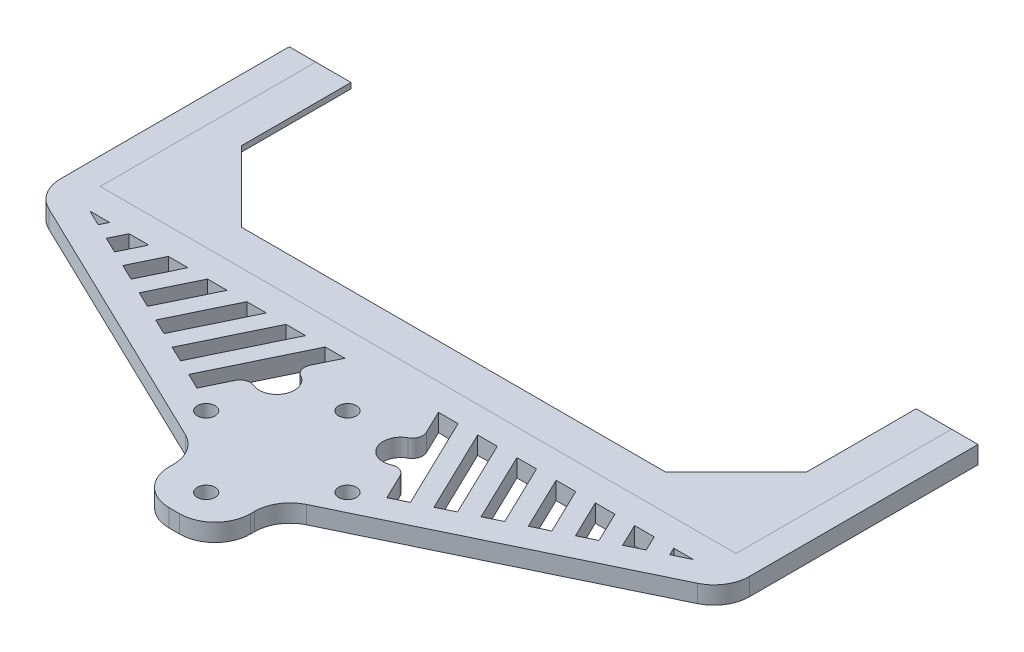
SolidWorks part; units mm, degrees
ref_plane "Front Plane" through (0, 0, 0) normal (0, 0, 1) x (1, 0, 0)
ref_plane "Top Plane" through (0, 0, 0) normal (0, 1, 0) x (1, 0, 0)
ref_plane "Right Plane" through (0, 0, 0) normal (1, 0, 0) x (0, 0, -1)
sketch "Sketch1" plane through (0, 0, 0) normal (0, 1, 0) x (1, 0, 0)
  line L0 (-114.3, 128.27) -> (-114.3, 50.8)
  line L1 (-114.3, 50.8) -> (114.3, 50.8)
  line L2 (114.3, 50.8) -> (114.3, 128.27)
  line L3 (114.3, 128.27) -> (123.825, 128.27)
  line L4 (123.825, 128.27) -> (123.825, 46.0729)
  line L5 (-114.3, 128.27) -> (-123.825, 128.27)
  line L6 (-123.825, 128.27) -> (-123.825, 46.0729)
  line L7 (0, 40) -> (0, -40) construction
  line L8 (-40, 0) -> (40, 0) construction
  line L9 (-28.2843, -28.2843) -> (28.2843, 28.2843) construction
  line L10 (-28.2843, 28.2843) -> (28.2843, -28.2843) construction
  line L11 (-116.6445, 34.635) -> (-21.7855, -11.14)
  line L13 (-14.605, -22.5779) -> (-14.605, -24.13)
  line L14 (-1.905, -36.83) -> (1.905, -36.83)
  line L15 (14.605, -24.13) -> (14.605, -22.5779)
  line L17 (21.7855, -11.14) -> (116.6445, 34.635)
  circle A0 centre (0, 0) radius 40 construction
  circle A1 centre (0, 0) radius 25.4 construction
  circle A2 centre (0, 0) radius 31.5 construction
  arc A3 (123.825, 46.0729) -> (116.6445, 34.635) centre (111.125, 46.0729) cw
  arc A4 (14.605, -22.5779) -> (21.7855, -11.14) centre (27.305, -22.5779) cw
  arc A5 (1.905, -36.83) -> (14.605, -24.13) centre (1.905, -24.13) ccw
  arc A6 (-14.605, -24.13) -> (-1.905, -36.83) centre (-1.905, -24.13) ccw
  arc A7 (-21.7855, -11.14) -> (-14.605, -22.5779) centre (-27.305, -22.5779) cw
  arc A8 (-123.825, 46.0729) -> (-116.6445, 34.635) centre (-111.125, 46.0729) ccw
  point P21 (0, 25.4)
  point P22 (25.4, 0)
  point P23 (0, -25.4)
  point P24 (-25.4, 0)
  point P25 (-22.2739, 22.2739)
  point P26 (-22.2739, -22.2739)
  point P27 (22.2739, -22.2739)
  point P28 (22.2739, 22.2739)
  point P37 (14.605, -14.605)
  point P40 (14.605, -36.83)
  point P43 (-14.605, -36.83)
  point P46 (-14.605, -14.605)
  point P49 (-123.825, 38.1)
  dimension "D4" = 80
  dimension "D5" = 50.8
  dimension "D6" = 63
  dimension "D13" = 12.7
  dimension "D1" = 247.65
  dimension "D2" = 9.525
  dimension "D3" = 9.525
  dimension "D7" = 45
  dimension "D8" = 77.47
  dimension "D9" = 29.21
  dimension "D10" = 50.8
  dimension "D11" = 11.43
  dimension "D12" = 12.7
extrude "Boss-Extrude1" add sketch "Sketch1" along normal blind 6.35
hole_wizard "M6 Clearance Hole1" positions "Sketch6" profile "Sketch5" hole size "M6" standard "ANSI Metric" end condition through all
sketch "Sketch6" plane through (0, 0, 0) normal (0, -1, 0) x (-1, 0, 0)
  point P0 (0, 25.4)
  point P3 (0, -25.4)
  point P6 (-25.4, 0)
  point P9 (25.4, 0)
sketch "Sketch5" plane through (0, 0, -25.4) normal (1, 0, 0) x (0, 0, -1)
  line L0 (0, 0) -> (0, 6.35)
  line L1 (0, 6.35) -> (3.2, 6.35)
  line L2 (3.2, 6.35) -> (3.2, 0)
  line L5 (3.2, 0) -> (0, 0)
  line L11 (0, -6.35) -> (0, 107.95) construction
  dimension "Thru Hole Dia." = 6.4
  dimension "Thru Hole Depth" = 6.35
sketch "Sketch7" plane through (0, 6.35, 0) normal (0, 1, 0) x (1, 0, 0)
  line L0 (-108.4879, 41.275) -> (-17.0471, -2.8505) construction
  line L1 (-108.4879, 41.275) -> (108.4879, 41.275) construction
  line L2 (108.4879, 41.275) -> (16.1645, -3.2765) construction
  line L3 (-62.7363, 19.1972) -> (-52.0825, 41.275)
  line L5 (-52.0825, 41.275) -> (-45.0318, 41.275)
  line L6 (-45.0318, 41.275) -> (-57.0174, 16.4375)
  line L8 (-57.0174, 16.4375) -> (-62.7363, 19.1972)
  line L9 (-114.3, 50.8) -> (114.3, 50.8) construction
  line L10 (-116.6445, 34.635) -> (-21.7855, -11.14) construction
  line L11 (21.7855, -11.14) -> (116.6445, 34.635) construction
  line L12 (-108.4879, 41.275) -> (-101.4373, 41.275)
  line L13 (-101.4373, 41.275) -> (-102.769, 38.5153)
  line L14 (-102.769, 38.5153) -> (-108.4879, 41.275)
  line L15 (-97.05, 35.7555) -> (-94.3866, 41.275)
  line L16 (-94.3866, 41.275) -> (-87.3359, 41.275)
  line L17 (-87.3359, 41.275) -> (-91.3311, 32.9958)
  line L18 (-91.3311, 32.9958) -> (-97.05, 35.7555)
  line L19 (-80.2852, 41.275) -> (-73.2345, 41.275)
  line L20 (-73.2345, 41.275) -> (-79.8932, 27.4764)
  line L21 (-79.8932, 27.4764) -> (-85.6121, 30.2361)
  line L22 (-85.6121, 30.2361) -> (-80.2852, 41.275)
  line L23 (-74.1742, 24.7166) -> (-66.1839, 41.275)
  line L24 (-66.1839, 41.275) -> (-59.1332, 41.275)
  line L25 (-59.1332, 41.275) -> (-68.4553, 21.9569)
  line L26 (-68.4553, 21.9569) -> (-74.1742, 24.7166)
  line L27 (-51.2984, 13.6777) -> (-37.9811, 41.275)
  line L28 (-37.9811, 41.275) -> (-30.9305, 41.275)
  line L29 (-30.9305, 41.275) -> (-45.5795, 10.918)
  line L30 (-45.5795, 10.918) -> (-51.2984, 13.6777)
  line L31 (-39.8605, 8.1583) -> (-23.8798, 41.275)
  line L32 (-23.8798, 41.275) -> (-16.8291, 41.275)
  line L33 (-16.8291, 41.275) -> (-20.8837, 32.8728)
  line L34 (-34.1416, 5.3986) -> (-39.8605, 8.1583)
  line L36 (-29.7059, 14.5905) -> (-34.1416, 5.3986)
  arc A1 (-19.2604, 27.8633) -> (-24.7743, 16.4369) centre (-22.2739, 22.2739) cw
  arc A2 (-24.7743, 16.4369) -> (-29.7059, 14.5905) centre (-26.2745, 12.9347) ccw
  arc A3 (-19.2604, 27.8633) -> (-20.8837, 32.8728) centre (-17.4523, 31.2169) cw
  dimension "D11" = 6.35
  dimension "D12" = 3.81
  dimension "D1" = 9.525
  dimension "D2" = 9.525
  dimension "D3" = 9.525
  dimension "D4" = 6.35
  dimension "D5" = 6.35
  dimension "D6" = 6.35
  dimension "D7" = 6.35
  dimension "D8" = 6.35
  dimension "D9" = 6.35
  dimension "D10" = 6.35
extrude "Cut-Extrude1" cut sketch "Sketch7" against normal through all
mirror "Mirror1" about plane through (0, 0, 0) normal (1, 0, 0) of "Cut-Extrude1"
sketch "Sketch8" plane through (0, 6.35, 0) normal (0, 1, 0) x (1, 0, 0)
  line L0 (114.3, 128.27) -> (101.6, 128.27)
  line L1 (101.6, 128.27) -> (101.6, 88.9)
  line L2 (-114.3, 128.27) -> (-114.3, 50.8)
  line L3 (-114.3, 50.8) -> (114.3, 50.8)
  line L4 (114.3, 128.27) -> (114.3, 50.8)
  line L5 (76.2, 63.5) -> (-76.2, 63.5)
  line L6 (-76.2, 63.5) -> (-101.6, 88.9)
  line L7 (-101.6, 128.27) -> (-114.3, 128.27)
  line L8 (101.6, 88.9) -> (76.2, 63.5)
  line L9 (-101.6, 88.9) -> (-101.6, 128.27)
  dimension "D1" = 12.7
  dimension "D2" = 12.7
  dimension "D3" = 12.7
  dimension "D4" = 25.4
  dimension "D5" = 25.4
extrude "Boss-Extrude2" add sketch "Sketch8" against normal blind 2 separate body
